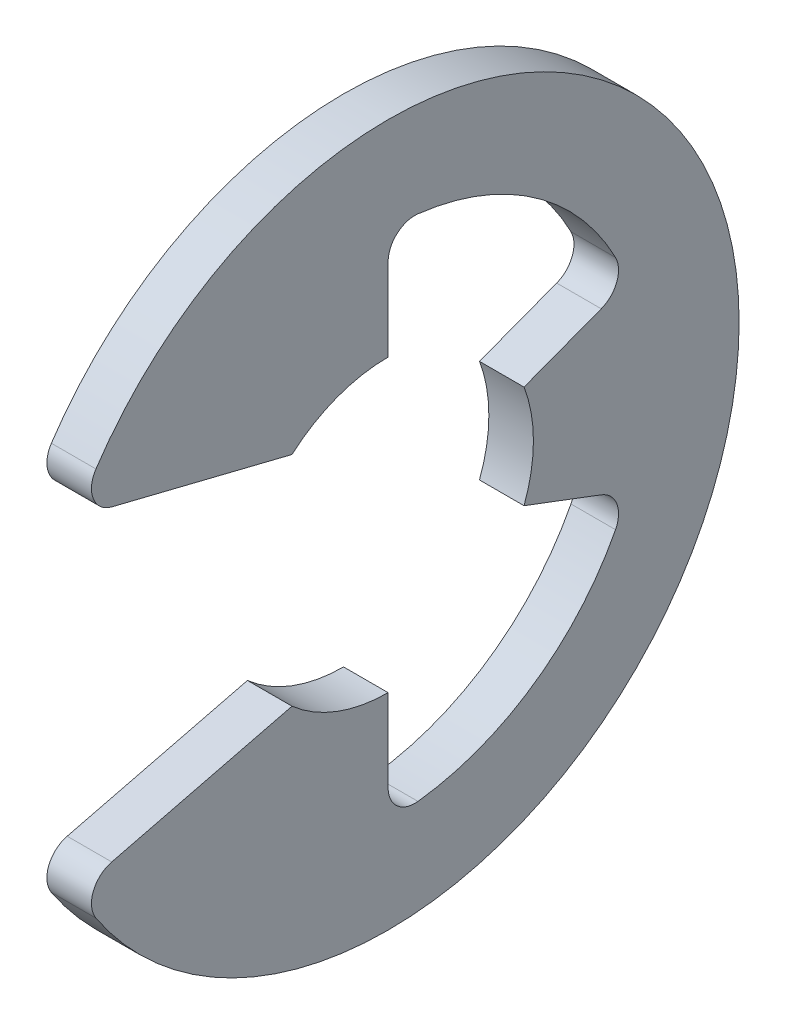
SolidWorks part; units mm, degrees
ref_plane "Front" through (0, 0, 0) normal (0, 0, 1) x (1, 0, 0)
ref_plane "Top" through (0, 0, 0) normal (0, 1, 0) x (1, 0, 0)
ref_plane "Right" through (0, 0, 0) normal (1, 0, 0) x (0, 0, -1)
sketch "Sketch1" plane through (0, 0, 0) normal (1, 0, 0) x (0, 0, -1)
  line L0 (-6.9817, -3.643) -> (-2.1563, -2.445)
  line L1 (-6.9817, 3.643) -> (-2.1563, 2.445)
  line L2 (0, -3.26) -> (0, -5.7471)
  line L3 (0, 3.26) -> (0, 5.7471)
  line L4 (3.0495, -1.1526) -> (5.3759, -2.0319)
  line L5 (3.0495, 1.1526) -> (5.3759, 2.0319)
  line L6 (0, 0) -> (-8.15, 0) construction
  line L7 (3.0495, 1.1526) -> (3.0495, -1.1526) construction
  line L8 (0, -3.26) -> (-2.1563, -2.445) construction
  circle A1 centre (0, 0) radius 8.15 construction
  circle A2 centre (0, 0) radius 3.26 construction
  arc A3 (-6.9817, -3.643) -> (-6.9817, 3.643) centre (0, 0) ccw
  arc A4 (-2.1563, -2.445) -> (0, -3.26) centre (0, 0) ccw
  arc A5 (-2.1563, 2.445) -> (0, 3.26) centre (0, 0) cw
  arc A6 (3.0495, 1.1526) -> (3.0495, -1.1526) centre (0, 0) cw
  arc A7 (0, -5.7471) -> (5.3759, -2.0319) centre (0, 0) ccw
  arc A8 (5.3759, 2.0319) -> (0, 5.7471) centre (0, 0) ccw
  dimension "D" = 6.52
  dimension "D1" = 5.7471
  dimension "OD" = 15.75
  dimension "D2" = 3.7068
  dimension "D3" = 4.89
extrude "Extrude1" add sketch "Sketch1" along normal mid plane 1
fillet "Fillet1" radius 0.6 6 edges at (0, -5.7471, 0) (0, 5.7471, 0) (0, -3.643, 6.9817) (0, 3.643, 6.9817) (0, -2.0319, -5.3759) (0, 2.0319, -5.3759)
sketch "Sketch3" plane through (0, 0, 0) normal (0, 1, 0) x (1, 0, 0)
  line L0 (0.525, 4.5) -> (0.525, 4)
  line L1 (0.525, 4) -> (-0.525, 4)
  line L2 (-0.525, 4) -> (-0.525, 4.5)
  line L3 (-0.525, 4.5) -> (-7.35, 4.5)
  line L4 (3.15, 0) -> (3.15, 4.25)
  line L5 (-7.35, 4.5) -> (-7.35, 0)
  line L6 (-7.35, 0) -> (3.15, 0)
  line L8 (3.15, 0) -> (3.15, 4.5) construction
  line L9 (3.15, 4.5) -> (0.525, 4.5) construction
  line L10 (3.15, 0) -> (17.2631, 0) construction
  line L11 (3.15, 4.25) -> (2.9, 4.5)
  line L12 (2.9, 4.5) -> (0.525, 4.5)
  point P2 (0, 4)
  point P5 (0.525, 4.25)
  dimension "D2" = 10.5
  dimension "D1" = 2.625
  dimension "D3" = 45
revolve "Revolve2" [suppressed] add sketch "Sketch3" angle 360 about L10
equation "\"D2@Sketch3\" = \"W@Sketch3\"*10"
equation "\"D1@Sketch3\" = \"D2@Sketch3\"/4"
equation "\"D1@Sketch1\" = (\"OD@Sketch1\"+\"D@Sketch1\")/3.875"
equation "\"D3@Sketch1\" = \"D@Sketch1\"*.75"
equation "\"D1@Fillet1\" = \"D1@Extrude1\"*.6"
